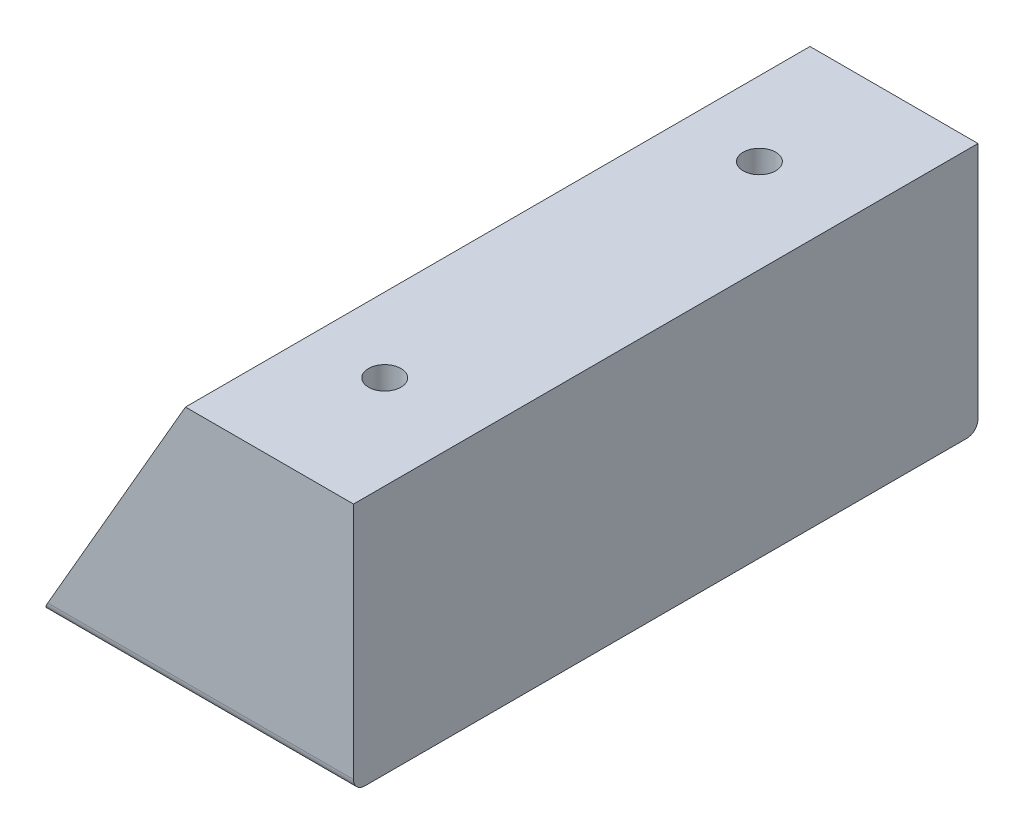
SolidWorks part; units mm, degrees
ref_plane "Front Plane" through (0, 0, 0) normal (0, 0, 1) x (1, 0, 0)
ref_plane "Top Plane" through (0, 0, 0) normal (0, 1, 0) x (1, 0, 0)
ref_plane "Right Plane" through (0, 0, 0) normal (1, 0, 0) x (0, 0, -1)
sketch "Sketch1" plane through (0, 0, 0) normal (0, 0, 1) x (1, 0, 0)
  line L0 (0, 0) -> (50, 0)
  line L1 (50, 0) -> (50, 40)
  line L2 (50, 40) -> (23.094, 40)
  line L3 (23.094, 40) -> (0, 0)
  dimension "D1" = 50
  dimension "D2" = 40
  dimension "D3" = 120
extrude "Boss-Extrude1" add sketch "Sketch1" along normal mid plane 100
sketch "Sketch2" plane through (0, 0, 0) normal (0, -1, 0) x (-1, 0, 0)
  line L3 (-50, -50) -> (-50, 50) construction
  line L4 (0, -50) -> (-50, -50) construction
  line L5 (0, 50) -> (-50, 50) construction
  line L6 (-50, -50) -> (-50, 50) construction
  circle A2 centre (-35, 30) radius 2.6
  circle A3 centre (-35, -30) radius 2.6
  dimension "D1" = 15
  dimension "D2" = 5.2
  dimension "D4" = 20
  dimension "D5" = 5.2
  dimension "D3" = 20
  dimension "D6" = 15
sketch "Sketch3" plane through (0, 40, 0) normal (0, 1, 0) x (1, 0, 0)
  line L0 (50, -50) -> (50, 50) construction
  circle A0 centre (35, 30) radius 2.6 construction
  circle A1 centre (35, 30) radius 2.6
  circle A2 centre (35, -30) radius 2.6 construction
  circle A3 centre (35, -30) radius 2.6
  dimension "D1" = 15
extrude "Cut-Extrude2" cut sketch "Sketch3" against normal blind 15
fillet "Fillet2" radius 1.8 1 edges at (25, 0, 50)
fillet "Fillet3" radius 1.8 1 edges at (25, 0, -50)
